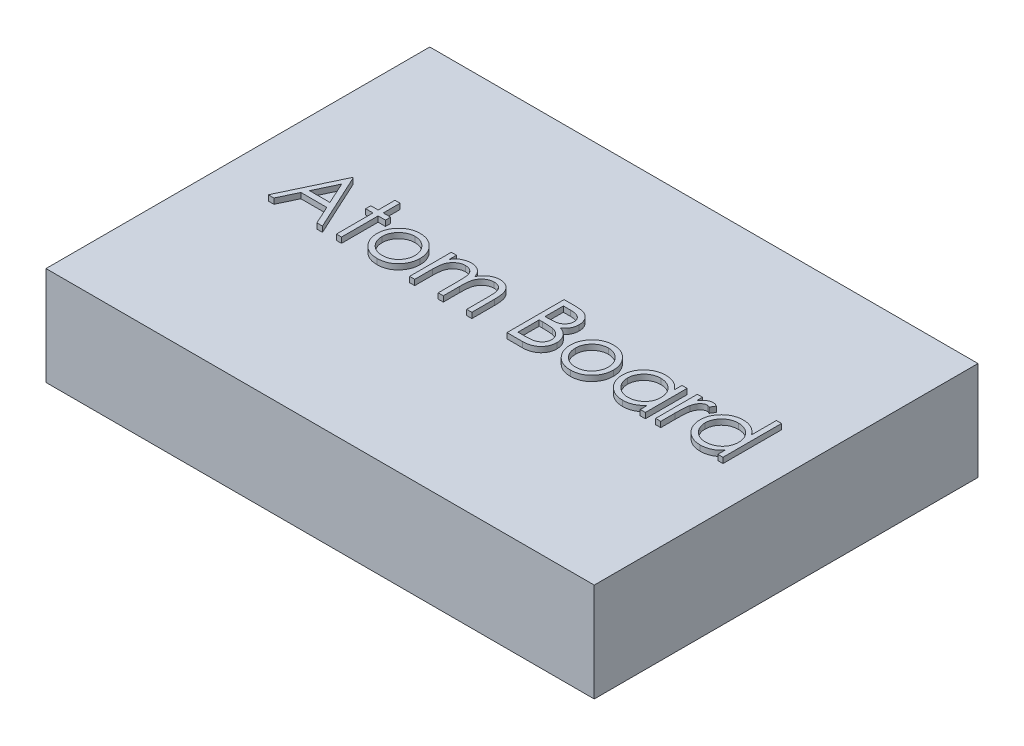
SolidWorks part; units mm, degrees
ref_plane "Front Plane" through (0, 0, 0) normal (0, 0, 1) x (1, 0, 0)
ref_plane "Top Plane" through (0, 0, 0) normal (0, 1, 0) x (1, 0, 0)
ref_plane "Right Plane" through (0, 0, 0) normal (1, 0, 0) x (0, 0, -1)
sketch "Sketch1" plane through (0, 0, 0) normal (0, 1, 0) x (1, 0, 0)
  line L1 (-127, -88.9) -> (127, -88.9)
  line L2 (-127, -88.9) -> (-127, 88.9)
  line L3 (-127, 88.9) -> (127, 88.9)
  line L4 (127, -88.9) -> (127, 88.9)
  line L5 (-127, -88.9) -> (127, 88.9) construction
  line L6 (-127, 88.9) -> (127, -88.9) construction
  point P0 (0, 0)
  dimension "D1" = 254
  dimension "D2" = 177.8
extrude "Boss-Extrude1" add sketch "Sketch1" along normal blind 45.72
sketch "Sketch2" plane through (0, 45.72, 0) normal (0, 1, 0) x (1, 0, 0)
  text T0 "Atom Board" font "Century Gothic" height in points 100
extrude "Boss-Extrude2" add sketch "Sketch2" along normal blind 2.54
